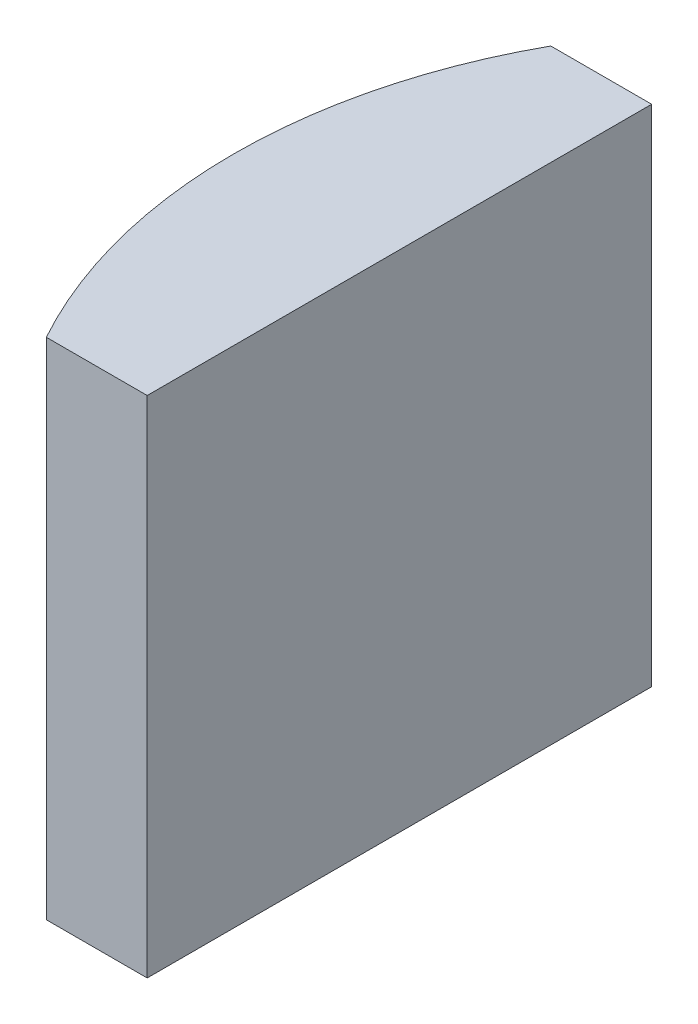
SolidWorks part; units mm, degrees
ref_plane "前视基准面" through (0, 0, 0) normal (0, 0, 1) x (1, 0, 0)
ref_plane "上视基准面" through (0, 0, 0) normal (0, 1, 0) x (1, 0, 0)
ref_plane "右视基准面" through (0, 0, 0) normal (1, 0, 0) x (0, 0, -1)
sketch "草图1" plane through (0, 0, 0) normal (0, 1, 0) x (1, 0, 0)
  line L0 (10.7432, 0) -> (-9.7696, 0) construction
  line L1 (-4.6841, 5) -> (-2.6848, 5)
  line L2 (-4.6841, -5) -> (-2.6848, -5)
  line L3 (-2.6848, 5) -> (-2.6848, -5)
  arc A0 (-4.6841, 5) -> (-4.6841, -5) centre (4.3552, 0) ccw
  point P2 (4.3467, 0)
  point P4 (4.3467, 0)
  point P8 (-10.0637, 0)
  point P10 (4.3552, 0)
  point P11 (-2.6848, 10)
  point P12 (0, 0)
  point P13 (4.3552, 0)
  point P14 (-9.7696, 0)
  point P15 (10.7432, 0)
  point P16 (-2.6848, -10)
  point P17 (4.3467, 0)
  point P18 (6.3318, -10)
  point P19 (-5.9748, 0)
  point P20 (-2.6848, 0)
  dimension "D2" = 5
  dimension "D3" = 10.33
  dimension "D4" = 3.29
  dimension "D1" = 5
extrude "凸台-拉伸1" add sketch "草图1" along normal blind 10
